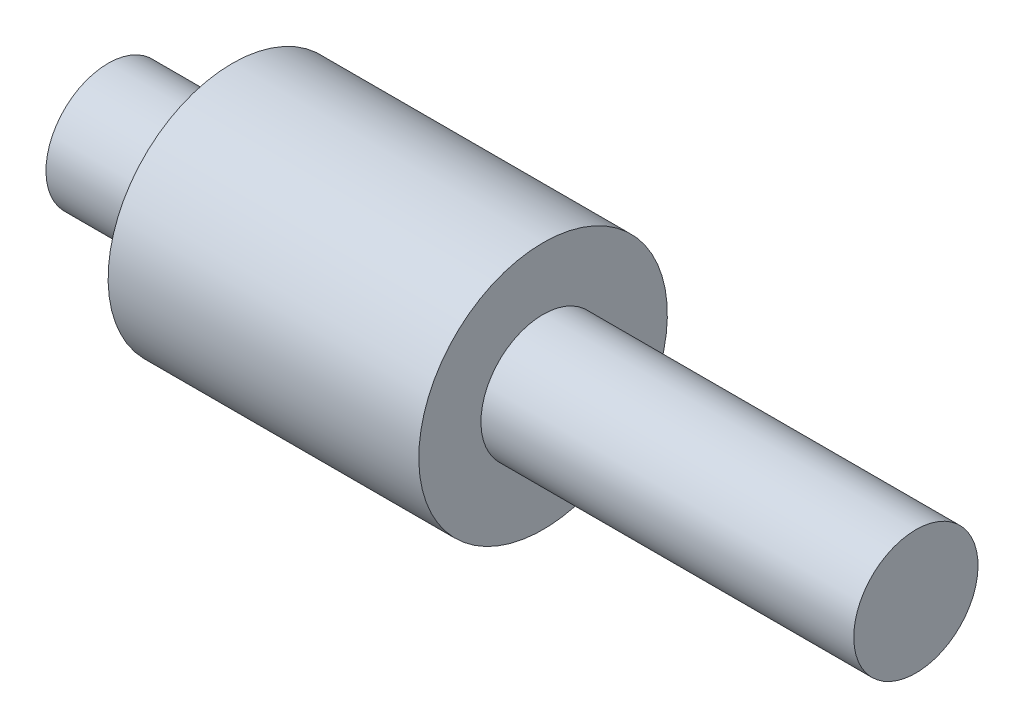
SolidWorks part; units mm, degrees
ref_plane "Front Plane" through (0, 0, 0) normal (0, 0, 1) x (1, 0, 0)
ref_plane "Top Plane" through (0, 0, 0) normal (0, 1, 0) x (1, 0, 0)
ref_plane "Right Plane" through (0, 0, 0) normal (1, 0, 0) x (0, 0, -1)
sketch "Sketch1" plane through (0, 0, 0) normal (0, 0, 1) x (1, 0, 0)
  line L0 (-35.7685, 5.1546) -> (-35.7685, 8.3296)
  line L1 (-35.7685, 8.3296) -> (-29.4185, 8.3296)
  line L2 (-29.4185, 8.3296) -> (-29.4185, 11.5046)
  line L3 (-29.4185, 11.5046) -> (-13.5435, 11.5046)
  line L4 (-13.5435, 11.5046) -> (-13.5435, 8.3296)
  line L5 (-13.5435, 8.3296) -> (5.5065, 8.3296)
  line L6 (5.5065, 8.3296) -> (5.5065, 5.1546)
  line L7 (5.5065, 5.1546) -> (-35.7685, 5.1546)
  dimension "D1" = 3.175
  dimension "D2" = 6.35
  dimension "D3" = 6.35
  dimension "D4" = 15.875
  dimension "D5" = 19.05
revolve "Revolve1" add sketch "Sketch1" angle 360 about L7
